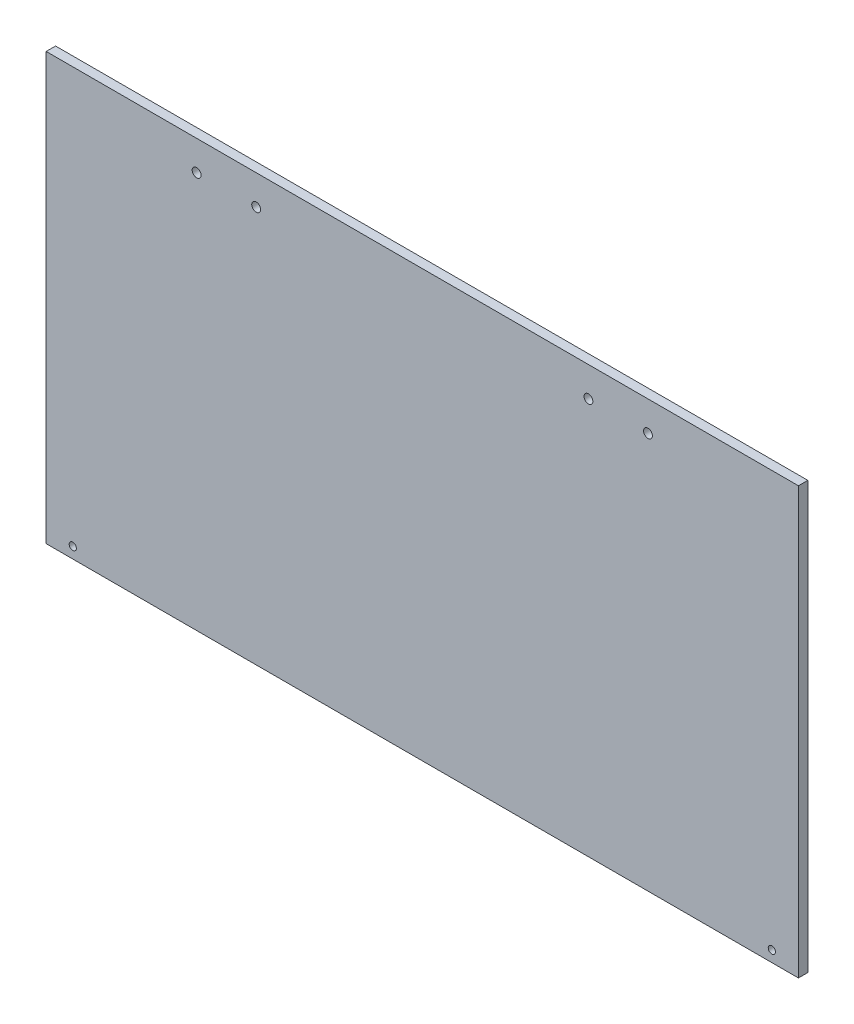
SolidWorks part; units mm, degrees
ref_plane "Front Plane" through (0, 0, 0) normal (0, 0, 1) x (1, 0, 0)
ref_plane "Top Plane" through (0, 0, 0) normal (0, 1, 0) x (1, 0, 0)
ref_plane "Right Plane" through (0, 0, 0) normal (1, 0, 0) x (0, 0, -1)
sketch "Sketch1" plane through (0, 0, 0) normal (0, 0, 1) x (1, 0, 0)
  line L1 (-190.5, 107.95) -> (190.5, 107.95)
  line L2 (-190.5, 107.95) -> (-190.5, -107.95)
  line L3 (-190.5, -107.95) -> (190.5, -107.95)
  line L4 (190.5, 107.95) -> (190.5, -107.95)
  line L5 (-190.5, 107.95) -> (190.5, -107.95) construction
  line L6 (-190.5, -107.95) -> (190.5, 107.95) construction
  point P0 (0, 0)
  dimension "D1" = 215.9
  dimension "D2" = 381
extrude "Boss-Extrude1" add sketch "Sketch1" along normal blind 4.7625
hole_wizard "#8 Clearance Hole1" positions "Sketch3" profile "Sketch2" hole size "#8" standard "ANSI Inch"
sketch "Sketch3" plane through (0, 0, 4.7625) normal (0, 0, 1) x (1, 0, 0)
  line L0 (190.5, 107.95) -> (-190.5, 107.95) construction
  line L1 (-190.5, 107.95) -> (-190.5, -107.95) construction
  line L2 (190.5, -107.95) -> (190.5, 107.95) construction
  point P0 (-114.3, 92.8688)
  point P2 (-84.1375, 92.8688)
  point P4 (84.1375, 92.8688)
  point P6 (114.3, 92.8688)
  dimension "D1" = 30.1625
  dimension "D2" = 30.1625
  dimension "D3" = 15.0812
  dimension "D4" = 76.2
  dimension "D5" = 76.2
sketch "Sketch2" plane through (-114.3, 92.8688, 4.7625) normal (1, 0, 0) x (0, -1, 0)
  line L0 (0, 0) -> (0, 75.7727)
  line L1 (0, 75.7727) -> (2.2479, 74.422)
  line L2 (2.2479, 74.422) -> (2.2479, 0)
  line L5 (2.2479, 0) -> (0, 0)
  line L10 (0, 75.7727) -> (-2.2479, 74.422) construction
  line L11 (0, -6.35) -> (0, 107.95) construction
  dimension "Hole Dia." = 4.4958
  dimension "Hole Depth" = 74.422
  dimension "Drill Angle" = 118
hole_wizard "#6 Clearance Hole1" positions "Sketch5" profile "Sketch4" hole size "#6" standard "ANSI Inch"
sketch "Sketch5" plane through (0, 0, 4.7625) normal (0, 0, 1) x (1, 0, 0)
  line L0 (-190.5, 107.95) -> (-190.5, -107.95) construction
  line L1 (190.5, -107.95) -> (190.5, 107.95) construction
  line L2 (-190.5, -107.95) -> (190.5, -107.95) construction
  point P0 (-177.0291, -102.362)
  point P2 (177.0291, -102.362)
  dimension "D1" = 13.4709
  dimension "D2" = 13.4709
  dimension "D3" = 5.588
sketch "Sketch4" plane through (-177.0291, -102.362, 4.7625) normal (1, 0, 0) x (0, -1, 0)
  line L0 (0, 0) -> (0, 75.5209)
  line L1 (0, 75.5209) -> (1.8288, 74.422)
  line L2 (1.8288, 74.422) -> (1.8288, 0)
  line L5 (1.8288, 0) -> (0, 0)
  line L10 (0, 75.5209) -> (-1.8288, 74.422) construction
  line L11 (0, -6.35) -> (0, 107.95) construction
  dimension "Hole Dia." = 3.6576
  dimension "Hole Depth" = 74.422
  dimension "Drill Angle" = 118
